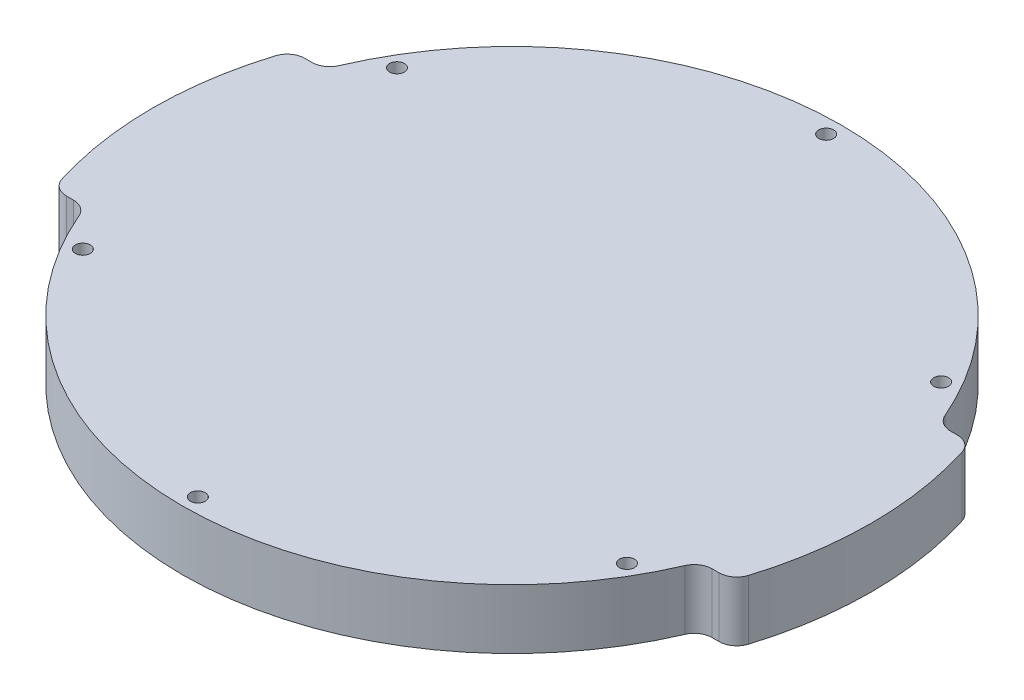
SolidWorks part; units mm, degrees
ref_plane "前视" through (0, 0, 0) normal (0, 0, 1) x (1, 0, 0)
ref_plane "上视" through (0, 0, 0) normal (0, 1, 0) x (1, 0, 0)
ref_plane "右视" through (0, 0, 0) normal (1, 0, 0) x (0, 0, -1)
sketch "草图3" plane through (0, 0, 0) normal (0, 1, 0) x (1, 0, 0)
  circle A0 centre (0, 0) radius 60.3
extrude "凸台-拉伸2" add sketch "草图3" along normal blind 10
sketch "草图4" plane through (0, 10, 0) normal (0, 1, 0) x (1, 0, 0)
  line L0 (-75.2656, 20) -> (82.2187, 20) construction
  line L1 (80.5383, -20) -> (-108.875, -20) construction
  line L2 (-51.5567, 20) -> (-56.8866, 20)
  line L3 (51.5567, 20) -> (56.8866, 20)
  line L4 (-56.8866, -20) -> (-51.5567, -20)
  line L5 (51.5567, -20) -> (56.8866, -20)
  arc A0 (51.5567, 20) -> (-51.5567, 20) centre (0, 0) ccw
  arc A1 (56.8866, 20) -> (-56.8866, 20) centre (0, 0) ccw
  circle A2 centre (0, 0) radius 60.3 construction
  arc A3 (-51.5567, -20) -> (51.5567, -20) centre (0, 0) ccw
  arc A4 (-56.8866, -20) -> (56.8866, -20) centre (0, 0) ccw
  dimension "D1" = 20
  dimension "D2" = 20
extrude "切除-拉伸2" cut sketch "草图4" against normal through all
fillet "圆角1" radius 3 8 edges at (51.5567, 5, -20) (56.8866, 5, -20) (56.8866, 5, 20) (51.5567, 5, 20) (-51.5567, 5, 20) (-56.8866, 5, 20) (-56.8866, 5, -20) (-51.5567, 5, -20)
sketch "草图5" plane through (0, 0, 0) normal (0, -1, 0) x (1, 0, 0)
  circle A0 centre (0, -52.7) radius 1.25
  arc A1 (-50.8147, -21.8165) -> (50.8147, -21.8165) centre (0, 0) ccw construction
  circle A2 centre (-45.6395, -26.35) radius 1.25
  circle A3 centre (-45.6395, 26.35) radius 1.25
  circle A4 centre (0, 52.7) radius 1.25
  circle A5 centre (45.6395, 26.35) radius 1.25
  circle A6 centre (45.6395, -26.35) radius 1.25
  point P2 (0, -55.3)
  point P19 (0, 0)
  dimension "D2" = 2.5
  dimension "D1" = 2.6
  dimension "D3" = 6
extrude "切除-拉伸3" cut sketch "草图5" against normal through all
